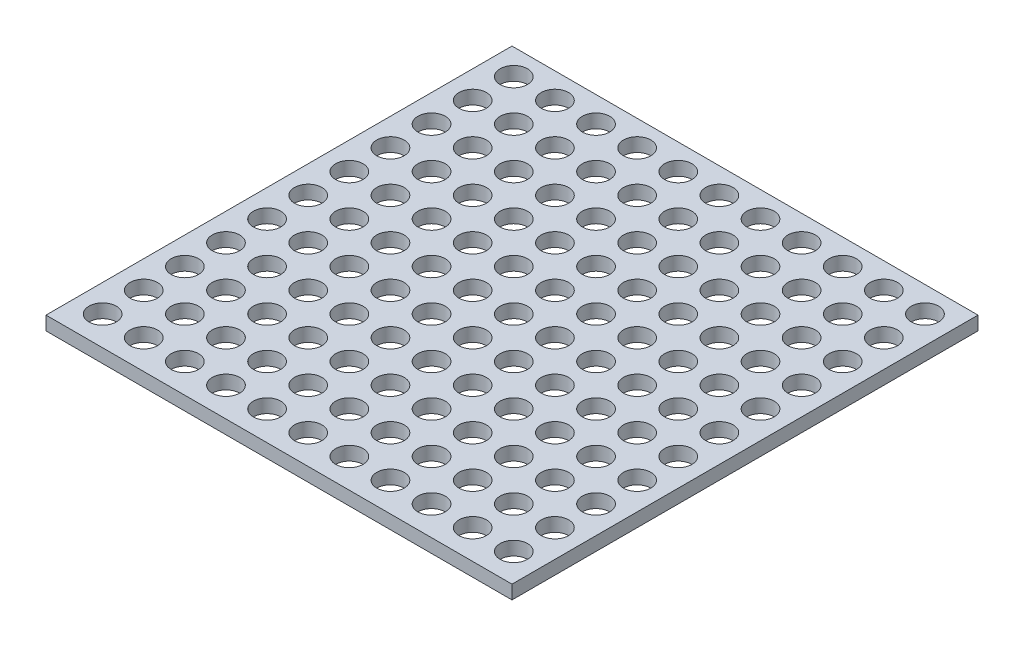
SolidWorks part; units mm, degrees
material "Balsa"
ref_plane "Front Plane" through (0, 0, 0) normal (0, 0, 1) x (1, 0, 0)
ref_plane "Top Plane" through (0, 0, 0) normal (0, 1, 0) x (1, 0, 0)
ref_plane "Right Plane" through (0, 0, 0) normal (1, 0, 0) x (0, 0, -1)
sketch "Sketch1" plane through (0, 0, 0) normal (0, 1, 0) x (1, 0, 0)
  line L1 (0, 1.2915) -> (107.95, 1.2915)
  line L2 (0, 1.2915) -> (0, 109.2415)
  line L3 (0, 109.2415) -> (107.95, 109.2415)
  line L4 (107.95, 1.2915) -> (107.95, 109.2415)
  line L5 (53.975, 109.2415) -> (53.975, 1.2915) construction
  line L6 (0, 55.2665) -> (107.95, 55.2665) construction
  circle A0 centre (6.35, 8.0565) radius 3.175
  circle A1 centre (15.875, 8.0565) radius 3.175
  circle A2 centre (25.4, 8.0565) radius 3.175
  circle A3 centre (34.925, 8.0565) radius 3.175
  circle A4 centre (44.45, 8.0565) radius 3.175
  circle A5 centre (53.975, 8.0565) radius 3.175
  circle A6 centre (63.5, 8.0565) radius 3.175
  circle A7 centre (73.025, 8.0565) radius 3.175
  circle A8 centre (82.55, 8.0565) radius 3.175
  circle A9 centre (92.075, 8.0565) radius 3.175
  circle A10 centre (101.6, 8.0565) radius 3.175
  circle A11 centre (101.6, 17.5815) radius 3.175
  circle A12 centre (92.075, 17.5815) radius 3.175
  circle A13 centre (82.55, 17.5815) radius 3.175
  circle A14 centre (73.025, 17.5815) radius 3.175
  circle A15 centre (63.5, 17.5815) radius 3.175
  circle A16 centre (53.975, 17.5815) radius 3.175
  circle A17 centre (44.45, 17.5815) radius 3.175
  circle A18 centre (34.925, 17.5815) radius 3.175
  circle A19 centre (25.4, 17.5815) radius 3.175
  circle A20 centre (15.875, 17.5815) radius 3.175
  circle A21 centre (6.35, 17.5815) radius 3.175
  circle A22 centre (101.6, 27.1065) radius 3.175
  circle A23 centre (92.075, 27.1065) radius 3.175
  circle A24 centre (82.55, 27.1065) radius 3.175
  circle A25 centre (73.025, 27.1065) radius 3.175
  circle A26 centre (63.5, 27.1065) radius 3.175
  circle A27 centre (53.975, 27.1065) radius 3.175
  circle A28 centre (44.45, 27.1065) radius 3.175
  circle A29 centre (34.925, 27.1065) radius 3.175
  circle A30 centre (25.4, 27.1065) radius 3.175
  circle A31 centre (15.875, 27.1065) radius 3.175
  circle A32 centre (6.35, 27.1065) radius 3.175
  circle A33 centre (101.6, 36.6315) radius 3.175
  circle A34 centre (92.075, 36.6315) radius 3.175
  circle A35 centre (82.55, 36.6315) radius 3.175
  circle A36 centre (73.025, 36.6315) radius 3.175
  circle A37 centre (63.5, 36.6315) radius 3.175
  circle A38 centre (53.975, 36.6315) radius 3.175
  circle A39 centre (44.45, 36.6315) radius 3.175
  circle A40 centre (34.925, 36.6315) radius 3.175
  circle A41 centre (25.4, 36.6315) radius 3.175
  circle A42 centre (15.875, 36.6315) radius 3.175
  circle A43 centre (6.35, 36.6315) radius 3.175
  circle A44 centre (101.6, 46.1565) radius 3.175
  circle A45 centre (92.075, 46.1565) radius 3.175
  circle A46 centre (82.55, 46.1565) radius 3.175
  circle A47 centre (73.025, 46.1565) radius 3.175
  circle A48 centre (63.5, 46.1565) radius 3.175
  circle A49 centre (53.975, 46.1565) radius 3.175
  circle A50 centre (44.45, 46.1565) radius 3.175
  circle A51 centre (34.925, 46.1565) radius 3.175
  circle A52 centre (25.4, 46.1565) radius 3.175
  circle A53 centre (15.875, 46.1565) radius 3.175
  circle A54 centre (6.35, 46.1565) radius 3.175
  circle A55 centre (101.6, 55.6815) radius 3.175
  circle A56 centre (92.075, 55.6815) radius 3.175
  circle A57 centre (82.55, 55.6815) radius 3.175
  circle A58 centre (73.025, 55.6815) radius 3.175
  circle A59 centre (63.5, 55.6815) radius 3.175
  circle A60 centre (53.975, 55.6815) radius 3.175
  circle A61 centre (44.45, 55.6815) radius 3.175
  circle A62 centre (34.925, 55.6815) radius 3.175
  circle A63 centre (25.4, 55.6815) radius 3.175
  circle A64 centre (15.875, 55.6815) radius 3.175
  circle A65 centre (6.35, 55.6815) radius 3.175
  circle A66 centre (101.6, 65.2065) radius 3.175
  circle A67 centre (92.075, 65.2065) radius 3.175
  circle A68 centre (82.55, 65.2065) radius 3.175
  circle A69 centre (73.025, 65.2065) radius 3.175
  circle A70 centre (63.5, 65.2065) radius 3.175
  circle A71 centre (53.975, 65.2065) radius 3.175
  circle A72 centre (44.45, 65.2065) radius 3.175
  circle A73 centre (34.925, 65.2065) radius 3.175
  circle A74 centre (25.4, 65.2065) radius 3.175
  circle A75 centre (15.875, 65.2065) radius 3.175
  circle A76 centre (6.35, 65.2065) radius 3.175
  circle A77 centre (101.6, 74.7315) radius 3.175
  circle A78 centre (92.075, 74.7315) radius 3.175
  circle A79 centre (82.55, 74.7315) radius 3.175
  circle A80 centre (73.025, 74.7315) radius 3.175
  circle A81 centre (63.5, 74.7315) radius 3.175
  circle A82 centre (53.975, 74.7315) radius 3.175
  circle A83 centre (44.45, 74.7315) radius 3.175
  circle A84 centre (34.925, 74.7315) radius 3.175
  circle A85 centre (25.4, 74.7315) radius 3.175
  circle A86 centre (15.875, 74.7315) radius 3.175
  circle A87 centre (6.35, 74.7315) radius 3.175
  circle A88 centre (101.6, 84.2565) radius 3.175
  circle A89 centre (92.075, 84.2565) radius 3.175
  circle A90 centre (82.55, 84.2565) radius 3.175
  circle A91 centre (73.025, 84.2565) radius 3.175
  circle A92 centre (63.5, 84.2565) radius 3.175
  circle A93 centre (53.975, 84.2565) radius 3.175
  circle A94 centre (44.45, 84.2565) radius 3.175
  circle A95 centre (34.925, 84.2565) radius 3.175
  circle A96 centre (25.4, 84.2565) radius 3.175
  circle A97 centre (15.875, 84.2565) radius 3.175
  circle A98 centre (6.35, 84.2565) radius 3.175
  circle A99 centre (101.6, 93.7815) radius 3.175
  circle A100 centre (92.075, 93.7815) radius 3.175
  circle A101 centre (82.55, 93.7815) radius 3.175
  circle A102 centre (73.025, 93.7815) radius 3.175
  circle A103 centre (63.5, 93.7815) radius 3.175
  circle A104 centre (53.975, 93.7815) radius 3.175
  circle A105 centre (44.45, 93.7815) radius 3.175
  circle A106 centre (34.925, 93.7815) radius 3.175
  circle A107 centre (25.4, 93.7815) radius 3.175
  circle A108 centre (15.875, 93.7815) radius 3.175
  circle A109 centre (6.35, 93.7815) radius 3.175
  circle A110 centre (101.6, 103.3065) radius 3.175
  circle A111 centre (92.075, 103.3065) radius 3.175
  circle A112 centre (82.55, 103.3065) radius 3.175
  circle A113 centre (73.025, 103.3065) radius 3.175
  circle A114 centre (63.5, 103.3065) radius 3.175
  circle A115 centre (53.975, 103.3065) radius 3.175
  circle A116 centre (44.45, 103.3065) radius 3.175
  circle A117 centre (34.925, 103.3065) radius 3.175
  circle A118 centre (25.4, 103.3065) radius 3.175
  circle A119 centre (15.875, 103.3065) radius 3.175
  circle A120 centre (6.35, 103.3065) radius 3.175
  point P120 (53.975, 55.2665)
  dimension "D3" = 6.35
  dimension "D1" = 107.95
  dimension "D2" = 107.95
  dimension "D4" = 11
  dimension "D5" = 11
extrude "Boss-Extrude1" add sketch "Sketch1" along normal blind 3.175
